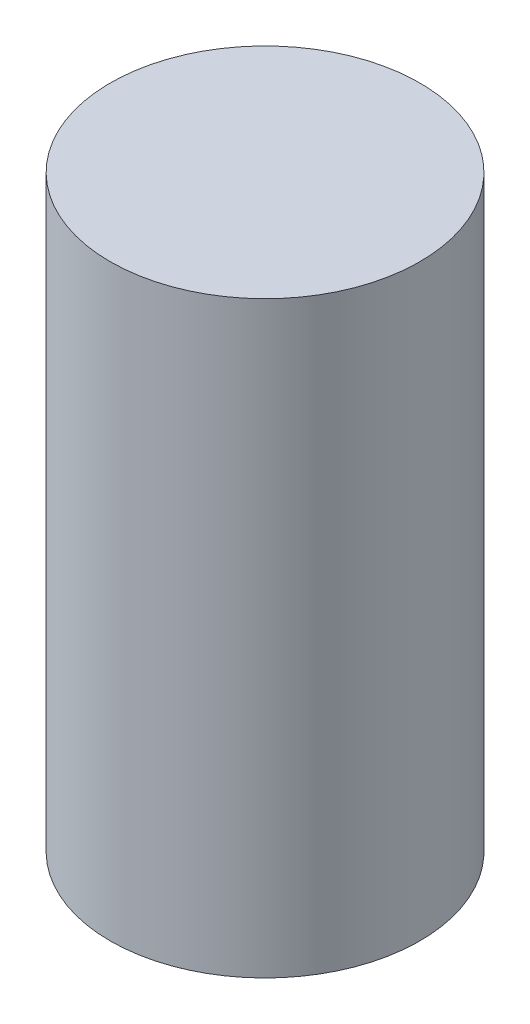
SolidWorks part; units mm, degrees
ref_plane "Front Plane" through (0, 0, 0) normal (0, 0, 1) x (1, 0, 0)
ref_plane "Top Plane" through (0, 0, 0) normal (0, 1, 0) x (1, 0, 0)
ref_plane "Right Plane" through (0, 0, 0) normal (1, 0, 0) x (0, 0, -1)
sketch "Sketch1" plane through (0, 0, 0) normal (0, 1, 0) x (1, 0, 0)
  circle A0 centre (0, 0) radius 5
  dimension "D1" = 10
extrude "Boss-Extrude1" add sketch "Sketch1" along normal blind 19
